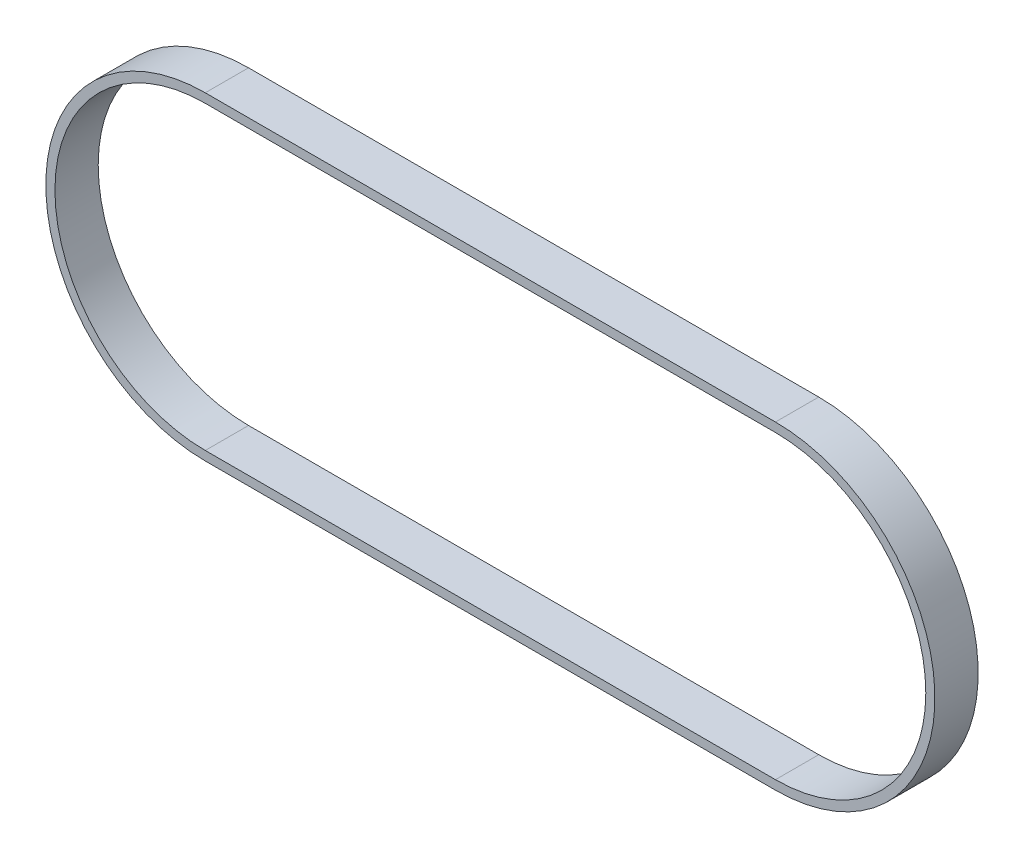
SolidWorks part; units mm, degrees
material "Rubber"
ref_plane "Front Plane" through (0, 0, 0) normal (0, 0, 1) x (1, 0, 0)
ref_plane "Top Plane" through (0, 0, 0) normal (0, 1, 0) x (1, 0, 0)
ref_plane "Right Plane" through (0, 0, 0) normal (1, 0, 0) x (0, 0, -1)
sketch "Sketch2" plane through (0, 0, 0) normal (0, 0, 1) x (1, 0, 0)
  line L0 (0, 0) -> (1, 0) construction
  line L1 (0, 0) -> (0, 1) construction
  line L2 (0, -34) -> (-125.18, -34)
  line L3 (-125.18, 34) -> (0, 34)
  arc A0 (0, 34) -> (0, -34) centre (0, 0) cw
  arc A1 (-125.18, -34) -> (-125.18, 34) centre (-125.18, 0) cw
extrude "Extrude-Thin2" add sketch "Sketch2" along normal blind 4.75 and the other way blind 4.75 thin thin type mid plane wall 2
